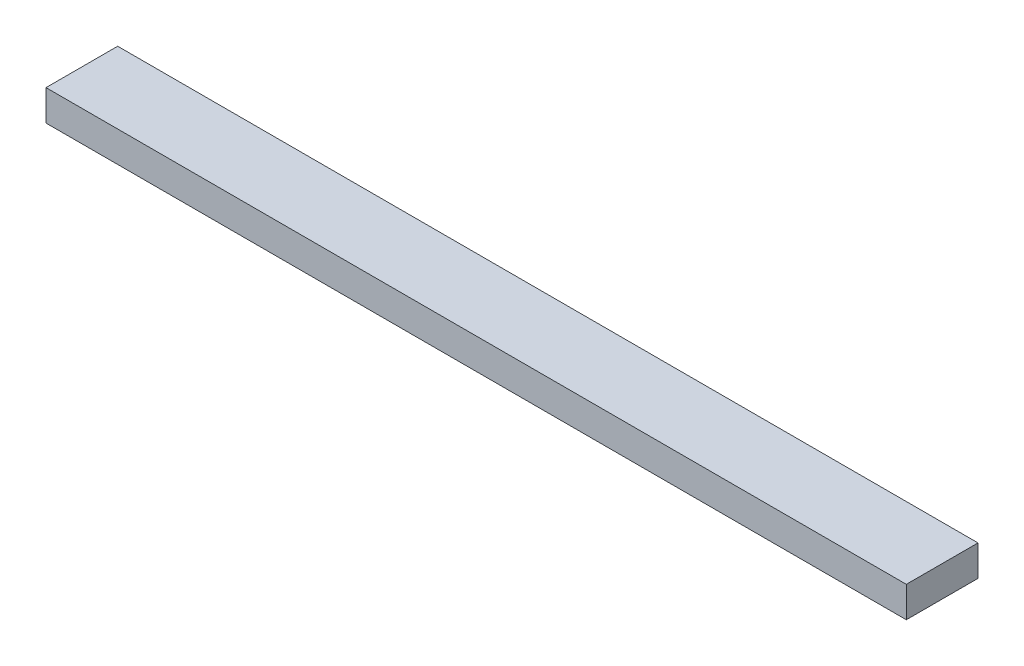
SolidWorks part; units mm, degrees
material "Pine"
ref_plane "Front Plane" through (0, 0, 0) normal (0, 0, 1) x (1, 0, 0)
ref_plane "Top Plane" through (0, 0, 0) normal (0, 1, 0) x (1, 0, 0)
ref_plane "Right Plane" through (0, 0, 0) normal (1, 0, 0) x (0, 0, -1)
sketch "Sketch1" plane through (0, 0, 0) normal (0, 1, 0) x (1, 0, 0)
  line L1 (0, 0) -> (1066.8, 0)
  line L2 (0, 0) -> (0, 88.9)
  line L3 (0, 88.9) -> (1066.8, 88.9)
  line L4 (1066.8, 0) -> (1066.8, 88.9)
  dimension "D1" = 88.9
  dimension "D2" = 1066.8
extrude "Boss-Extrude1" add sketch "Sketch1" along normal blind 38.1
